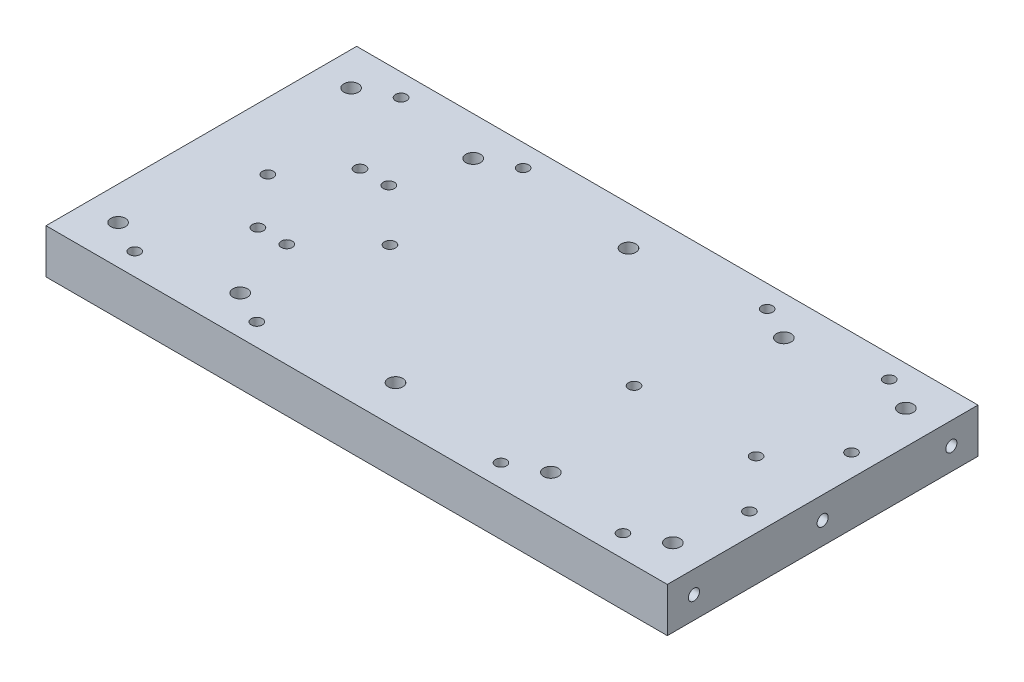
SolidWorks part; units mm, degrees
material "1023 Листовая углеродистая сталь (SS)"
ref_plane "Front" through (0, 0, 0) normal (0, 0, 1) x (1, 0, 0)
ref_plane "Top" through (0, 0, 0) normal (0, 1, 0) x (1, 0, 0)
ref_plane "Right" through (0, 0, 0) normal (1, 0, 0) x (0, 0, -1)
sketch "Sketch1" plane through (0, 0, 0) normal (0, 1, 0) x (1, 0, 0)
  line L1 (-140, 70) -> (140, 70)
  line L2 (-140, 70) -> (-140, -70)
  line L3 (-140, -70) -> (140, -70)
  line L4 (140, 70) -> (140, -70)
  line L5 (-140, 70) -> (140, -70) construction
  line L6 (-140, -70) -> (140, 70) construction
  point P0 (0, 0)
  dimension "D1" = 140
  dimension "D2" = 280
extrude "Extrude1" add sketch "Sketch1" along normal blind 20
hole_wizard "M6 Tapped Hole1" positions "Sketch2" profile "Sketch3" tap size "M6" standard "DIN" end condition through all
sketch "Sketch2" plane through (0, 0, 0) normal (0, -1, 0) x (-1, 0, 0)
  point P0 (-110, 60)
  point P3 (-55, 60)
  point P6 (-110, 0)
  point P9 (-55, 0)
  point P12 (-110, -60)
  point P15 (-55, -60)
  point P18 (55, 60)
  point P21 (110, 60)
  point P24 (110, 0)
  point P26 (55, 0)
  point P29 (110, -60)
  point P32 (55, -60)
sketch "Sketch3" plane through (110, 0, -60) normal (1, 0, 0) x (0, 0, -1)
  line L0 (0, 0) -> (0, 20)
  line L1 (0, 20) -> (2.5, 20)
  line L2 (2.5, 20) -> (2.5, 0)
  line L5 (2.5, 0) -> (0, 0)
  line L11 (0, -6.35) -> (0, 107.95) construction
  dimension "Диаметр проходного сверла" = 5
  dimension "Глубина проходного сверла" = 20
cosmetic thread "Cosmetic Thread7" parameters "D2"=6
cosmetic thread "Cosmetic Thread8" parameters "D2"=6
cosmetic thread "Cosmetic Thread9" parameters "D2"=6
cosmetic thread "Cosmetic Thread10" parameters "D2"=6
cosmetic thread "Cosmetic Thread11" parameters "D2"=6
cosmetic thread "Cosmetic Thread12" parameters "D2"=6
cosmetic thread "Cosmetic Thread13" parameters "D2"=6
cosmetic thread "Cosmetic Thread15" parameters "D2"=6
cosmetic thread "Cosmetic Thread18" parameters "D2"=6
cosmetic thread "Cosmetic Thread19" parameters "D2"=6
cosmetic thread "Cosmetic Thread20" parameters "D2"=6
cosmetic thread "Cosmetic Thread21" parameters "D2"=6
hole_wizard "M6 Tapped Hole2" positions "Sketch4" profile "Sketch5" tap size "M6" standard "DIN" end condition through all
sketch "Sketch4" plane through (0, 20, 0) normal (0, 1, 0) x (1, 0, 0)
  point P2 (-91.5, 23)
  point P5 (-78.5, 23)
  point P8 (-91.5, -23)
  point P11 (-78.5, -23)
  point P14 (130, 23)
  point P17 (130, -23)
sketch "Sketch5" plane through (-91.5, 20, -23) normal (1, 0, 0) x (0, 0, 1)
  line L0 (0, 0) -> (0, 20)
  line L1 (0, 20) -> (2.5, 20)
  line L2 (2.5, 20) -> (2.5, 0)
  line L5 (2.5, 0) -> (0, 0)
  line L11 (0, -6.35) -> (0, 107.95) construction
  dimension "Диаметр проходного сверла" = 5
  dimension "Глубина проходного сверла" = 20
cosmetic thread "Cosmetic Thread22" parameters "D2"=6
cosmetic thread "Cosmetic Thread23" parameters "D2"=6
cosmetic thread "Cosmetic Thread24" parameters "D2"=6
cosmetic thread "Cosmetic Thread25" parameters "D2"=6
cosmetic thread "Cosmetic Thread26" parameters "D2"=6
cosmetic thread "Cosmetic Thread27" parameters "D2"=6
hole_wizard "M6 Tapped Hole3" positions "Sketch6" profile "Sketch7" tap size "M6" standard "DIN"
sketch "Sketch6" plane through (140, 0, 0) normal (1, 0, 0) x (0, 0, -1)
  point P0 (-58, 10)
  point P3 (0, 10)
  point P6 (58, 10)
cosmetic thread "Cosmetic Thread28" parameters "D1"=280, "D2"=6
cosmetic thread "Cosmetic Thread29" parameters "D1"=280, "D2"=6
cosmetic thread "Cosmetic Thread30" parameters "D1"=280, "D2"=6
sketch "Sketch7" plane through (140, 10, 58) normal (0, 1, 0) x (0, 0, -1)
  line L0 (0, 0) -> (0, 26.5022)
  line L1 (0, 26.5022) -> (2.5, 25)
  line L2 (2.5, 25) -> (2.5, 0)
  line L5 (2.5, 0) -> (0, 0)
  line L10 (0, 26.5022) -> (-2.5, 25) construction
  line L11 (0, -6.35) -> (0, 107.95) construction
  dimension "Диаметр сверла" = 5
  dimension "Глубина сверла" = 25
  dimension "Угол заточки сверла" = 118
hole_wizard "CBORE for M6 Hex Socket Thin Head Cap Screw1" positions "Sketch8" profile "Sketch9" counterbore size "M6" standard "DIN" end condition through all
sketch "Sketch8" plane through (0, 0, 0) normal (0, -1, 0) x (-1, 0, 0)
  line L0 (-140, 70) -> (140, 70) construction
  line L1 (-140, -70) -> (-140, 70) construction
  line L2 (0, 0) -> (-28.9506, 0) construction
  line L3 (0, 0) -> (0, -21.0385) construction
  point P0 (-125, 52.5)
  point P2 (-70, 52.5)
  point P4 (0, 52.5)
  point P19 (0, -52.5)
  point P20 (-70, -52.5)
  point P21 (-125, -52.5)
  point P27 (125, -52.5)
  point P28 (70, -52.5)
  point P29 (70, 52.5)
  point P30 (125, 52.5)
  dimension "D1" = 17.5
  dimension "D2" = 15
  dimension "D3" = 70
sketch "Sketch9" plane through (125, 0, -52.5) normal (1, 0, 0) x (0, 0, -1)
  line L0 (0, 0) -> (0, 20)
  line L1 (0, 20) -> (3.3, 20)
  line L3 (3.3, 20) -> (3.3, 4.6)
  line L4 (3.3, 4.6) -> (5.5, 4.6)
  line L5 (5.5, 4.6) -> (5.5, 0)
  line L7 (5.5, 0) -> (0, 0)
  line L11 (0, -6.35) -> (0, 107.95) construction
  dimension "Диаметр сквозного отверстия" = 6.6
  dimension "Глубина сквозного отверстия" = 20
  dimension "Диаметр цековки" = 11
  dimension "Глубина цековки" = 4.6
hole_wizard "M6 Tapped Hole4" positions "Sketch10" profile "Sketch11" tap size "M6" standard "DIN"
sketch "Sketch10" plane through (-140, 0, 0) normal (-1, 0, 0) x (0, 0, 1)
  point P0 (58, 10)
  point P3 (0, 10)
  point P6 (-58, 10)
sketch "Sketch11" plane through (-140, 10, 58) normal (0, 1, 0) x (0, 0, 1)
  line L0 (0, 0) -> (0, 26.5022)
  line L1 (0, 26.5022) -> (2.5, 25)
  line L2 (2.5, 25) -> (2.5, 0)
  line L5 (2.5, 0) -> (0, 0)
  line L10 (0, 26.5022) -> (-2.5, 25) construction
  line L11 (0, -6.35) -> (0, 107.95) construction
  dimension "Диаметр сверла" = 5
  dimension "Глубина сверла" = 25
  dimension "Угол заточки сверла" = 118
cosmetic thread "Cosmetic Thread31" parameters "D1"=24, "D2"=6
cosmetic thread "Cosmetic Thread32" parameters "D1"=24, "D2"=6
cosmetic thread "Cosmetic Thread33" parameters "D1"=24, "D2"=6
